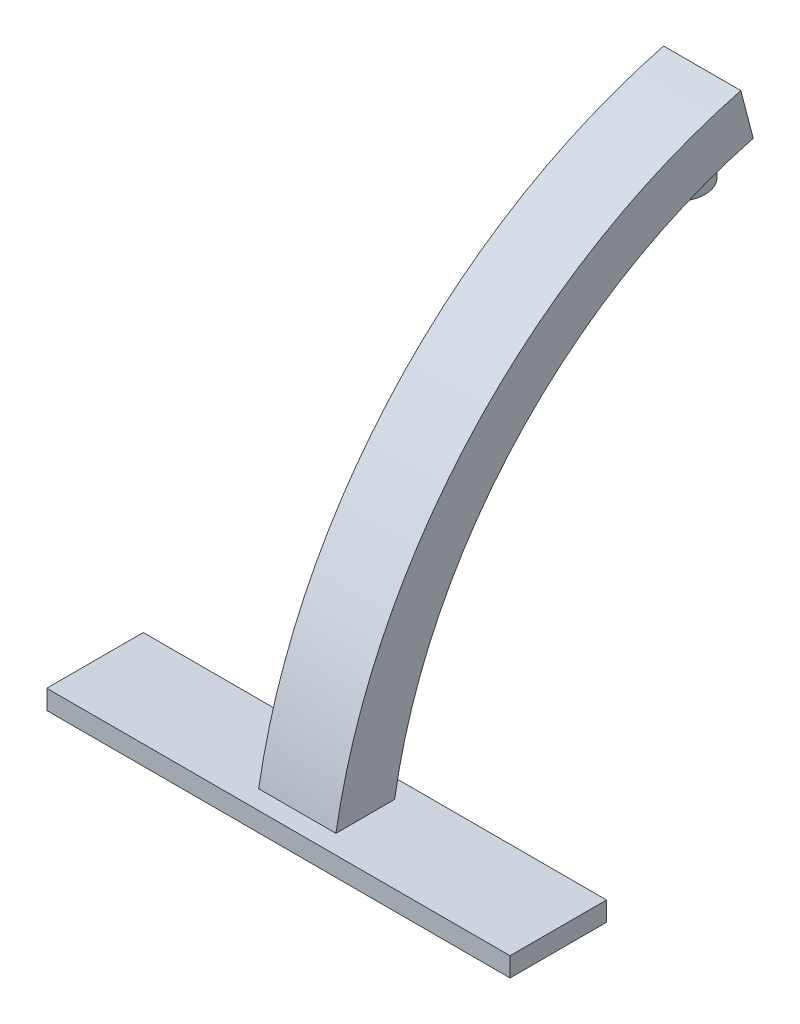
SolidWorks part; units mm, degrees
ref_plane "Front Plane" through (0, 0, 0) normal (0, 0, 1) x (1, 0, 0)
ref_plane "Top Plane" through (0, 0, 0) normal (0, 1, 0) x (1, 0, 0)
ref_plane "Right Plane" through (0, 0, 0) normal (1, 0, 0) x (0, 0, -1)
ref_plane "Plane1" through (0, 0, 0) normal (0, 1, 0) x (1, 0, 0)
sketch "Sketch1" plane through (0, 0, 0) normal (0, 1, 0) x (1, 0, 0)
  line L1 (0, 0) -> (152.4, 0)
  line L2 (0, 0) -> (0, 31.75)
  line L3 (0, 31.75) -> (152.4, 31.75)
  line L4 (152.4, 0) -> (152.4, 31.75)
  dimension "D1" = 31.75
  dimension "D2" = 152.4
extrude "Boss-Extrude1" add sketch "Sketch1" along normal blind 6.35
ref_plane "Plane2" through (76.2, 0, 0) normal (1, 0, 0) x (0, 0, -1)
sketch "Sketch5" plane through (76.2, 0, 0) normal (1, 0, 0) x (0, 0, -1)
  line L0 (0, 6.35) -> (31.75, 6.35) construction
  line L1 (6.2181, 6.35) -> (25.5319, 6.35)
  line L2 (139.4185, 151.35) -> (143.5006, 135.6926)
  arc A0 (6.2181, 6.35) -> (139.4185, 151.35) centre (185.2464, -24.4291) cw
  arc A1 (143.5006, 135.6926) -> (25.5319, 6.35) centre (184.0226, -19.7348) ccw
  point P0 (15.875, 6.35)
  point P4 (15.875, 6.35)
extrude "Boss-Extrude2" add sketch "Sketch5" along normal blind 12.7 and the other way blind 12.7 contours L1 A1 L2 A0
sketch "Sketch6" plane through (0, 0, 0) normal (0, 1, 0) x (1, 0, 0)
  line L0 (152.4, 31.75) -> (0, 31.75) construction
  circle A0 centre (76.2, 130.81) radius 9.525
  dimension "D1" = 99.06
ref_plane "Plane3" through (0, 137.16, 0) normal (0, 1, 0) x (1, 0, 0)
sketch "Sketch7" plane through (0, 137.16, 0) normal (0, 1, 0) x (1, 0, 0)
  circle A0 centre (76.2, 130.81) radius 9.525
extrude "Boss-Extrude4" add sketch "Sketch7" against normal blind 12.7
ref_plane "Plane4" through (0, 0, -19.05) normal (0, 0, -1) x (-1, 0, 0)
sketch "Sketch8" plane through (0, 0, -19.05) normal (0, 0, -1) x (-1, 0, 0)
  line L0 (-88.9, 135.6926) -> (-88.9, 6.35) construction
  line L1 (-85.09, 38.1) -> (-67.31, 38.1)
  line L2 (-85.09, 38.1) -> (-85.09, 12.7)
  line L3 (-85.09, 12.7) -> (-67.31, 12.7)
  line L4 (-67.31, 38.1) -> (-67.31, 12.7)
  line L5 (-63.5, 6.35) -> (-63.5, 135.6926) construction
  line L6 (-152.4, 6.35) -> (0, 6.35) construction
  dimension "D1" = 3.81
  dimension "D2" = 3.81
  dimension "D3" = 6.35
  dimension "D4" = 25.4
extrude "Boss-Extrude5" add sketch "Sketch8" along normal offset from surface (16.4853 mm away) 1.27
